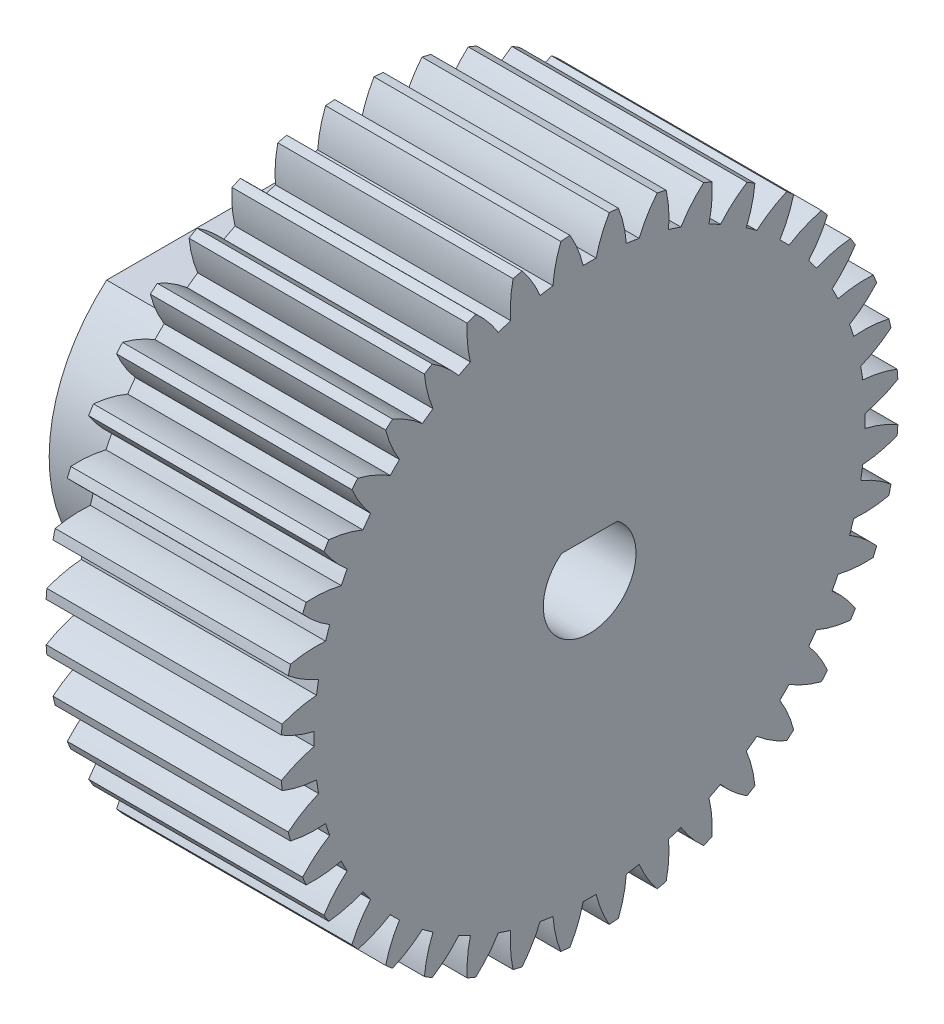
SolidWorks part; units mm, degrees
ref_plane "Plane1" through (0, 0, 0) normal (0, 0, 1) x (1, 0, 0)
ref_plane "Plane2" through (0, 0, 0) normal (0, 1, 0) x (1, 0, 0)
ref_plane "Plane3" through (0, 0, 0) normal (1, 0, 0) x (0, 0, -1)
sketch "HoldingSke" plane through (0, 0, 0) normal (0, 1, 0) x (1, 0, 0)
  line L0 (0, 0) -> (622.6409, -522.4578)
  line L1 (-15, 0) -> (100, 0) construction
  line L2 (0, 0) -> (-2.1039, 2.3779)
  line L3 (0, 0) -> (-11.863, 4.5341)
  line L4 (0, 0) -> (6.6156, 5.5511)
  line L5 (0, 0) -> (-47.5972, -17.7524)
  line L6 (0, 0) -> (-10.5278, -7.1032)
  line L7 (-2.1039, 2.3779) -> (8.8308, 51.9871)
  line L8 (-76.2, 54.61) -> (-71.1708, 54.61)
  line L9 (-71.009, 38.7566) -> (-53.1078, 45.2721)
  line L10 (-76.2, 71.12) -> (104.1128, 71.12)
  line L11 (0, 0) -> (-12.7, 0)
  line L12 (-76.2, 101.6) -> (-76.1716, 101.6)
  line L13 (24.9733, 27.94) -> (52.9518, 28.4284)
  line L14 (24.9733, 27.94) -> (25.0241, 27.9398)
  line L15 (24.9733, 27.94) -> (100.4021, 29.52)
  circle A0 centre (0, 0) radius 2.3812
  circle A1 centre (0, 0) radius 14.8717
  circle A2 centre (0, 0) radius 38.1
  circle A3 centre (0, 0) radius 2.3812
  dimension "MHD" = 29.7434
  dimension "Hub_dia" = 76.2
  dimension "Bore" = 4.7625
  dimension "MBD" = 4.7625
  dimension "Num_teeth" = 40
  dimension "Pitch" = 812.8
  dimension "Overall_len" = 50.8
  dimension "Show_teeth" = 40
  dimension "Thickness" = 12.7
  dimension "OAL" = 50.8001
  dimension "T_dim" = 5.0292
  dimension "Ap" = 20
  dimension "H" = 19.05
  dimension "Pitch_radius" = 180.3128
  dimension "Width" = 12.7
  dimension "Backlash" = 0.0284
  dimension "Addendum_fac" = 1
  dimension "Dedendum_fac" = 1.2
  dimension "Clearance_fac" = 0.2
  dimension "Dedendum_add" = 0.0508
sketch "BasProSke" plane through (0, 0, 0) normal (0, 1, 0) x (1, 0, 0)
  line L0 (-10, 0) -> (60, 0) construction
  line L1 (0, 0) -> (0, 16.6687)
  line L2 (0, 0) -> (12.7, 0)
  line L3 (12.7, 0) -> (12.7, 16.6687)
  line L4 (12.7, 16.6687) -> (0, 16.6687)
  dimension "Thickness" = 12.7
  dimension "Diameter" = 33.3375
revolve "Base-Revolve" add sketch "BasProSke" angle 360 about L0
sketch "TooCutSke" plane through (0, 0, 0) normal (1, 0, 0) x (0, 0, -1)
  line L1 (0, 0) -> (0, 107) construction
  line L2 (0, 0) -> (-0.673, 15.8607) construction
  line L3 (0, 0) -> (-2.4895, 31.6315) construction
  line L4 (-0.673, 15.8607) -> (-1.2447, 15.8157) construction
  arc A0 (0.3509, 14.8676) -> (-0.3509, 14.8676) centre (0, 0) ccw
  arc A1 (1.0752, 16.6595) -> (-1.0752, 16.6595) centre (0, 0) ccw
  circle A2 centre (0, 0) radius 15.875 construction
  circle A3 centre (0, 0) radius 14.9176 construction
  arc A4 (-0.3509, 14.8676) -> (-1.0752, 16.6595) centre (-6.5317, 13.4116) ccw
  arc A5 (1.0752, 16.6595) -> (0.3509, 14.8676) centre (6.5317, 13.4116) ccw
  dimension "Root_dia" = 29.7434
  dimension "Overcut_dia" = 33.3883
  dimension "Pitch_dia" = 31.75
  dimension "Base_dia" = 29.8352
  dimension "Flank_rad" = 6.35
  dimension "Half_ang" = 4.5
  dimension "Half_CT" = 0.5735
extrude "ToothCut" cut sketch "TooCutSke" along normal through all
fillet "Breaks" [suppressed] radius 0.0159
fillet "RootFillets" [suppressed] radius 0.2095
pattern_circular "TeethCuts" count 40 every 9 about axis through (-10, 0, 0) along (1, 0, 0) of "ToothCut", "RootFillets", "Breaks"
sketch "HubNeaOneSke" plane through (0, 0, 0) normal (-1, 0, 0) x (0, 0, 1)
  circle A0 centre (0, 0) radius 14.8717
  dimension "Diameter" = 29.7434
extrude "HubNearOne" [suppressed] add sketch "HubNeaOneSke" along normal blind 38.1001
sketch "HubNeaBotSke" plane through (0, 0, 0) normal (-1, 0, 0) x (0, 0, 1)
  circle A0 centre (0, 0) radius 14.8717
  dimension "Diameter" = 29.7434
extrude "HubNearBoth" [suppressed] add sketch "HubNeaBotSke" along normal blind 19.05
ref_plane "FarPln" through (12.7, 0, 0) normal (1, 0, 0) x (0, 0, -1)
sketch "HubFarSke" plane through (12.7, 0, 0) normal (1, 0, 0) x (0, 0, -1)
  circle A0 centre (0, 0) radius 14.8717
  dimension "Diameter" = 29.7434
extrude "HubFar" [suppressed] add sketch "HubFarSke" along normal blind 19.05
sketch "BorSke" plane through (0, 0, 0) normal (1, 0, 0) x (0, 0, -1)
  circle A0 centre (0, 0) radius 2.3812
  dimension "Diameter" = 4.7625
extrude "Bore" cut sketch "BorSke" along normal mid plane 101.6001
sketch "KeySke" plane through (0, 0, 0) normal (1, 0, 0) x (0, 0, -1)
  line L0 (-0.127, 0) -> (-0.127, 2.6479)
  line L1 (-0.127, 2.6479) -> (0.127, 2.6479)
  line L2 (0.127, 2.6479) -> (0.127, 0)
  line L3 (0, 0) -> (0, 34) construction
  line L4 (-0.127, 0) -> (0.127, 0)
  dimension "Offset" = 2.648
  dimension "Width" = 0.254
extrude "Keyway" [suppressed] cut sketch "KeySke" along normal mid plane 101.6001
pattern_circular "Keyway2" [suppressed] count 2 every 90 about axis through (-10, 0, 0) along (1, 0, 0)
sketch "Sketch1" plane through (12.7, 0, 0) normal (1, 0, 0) x (0, 0, -1)
  line L0 (0, 25.6558) -> (0, -26.1333) construction
  line L1 (-24.8431, 0) -> (25.1424, 0) construction
  line L2 (-20.32, 20.32) -> (-20.32, -20.32) construction
  line L3 (-20.32, -20.32) -> (20.32, -20.32) construction
  line L4 (20.32, -20.32) -> (20.32, 20.32) construction
  line L5 (20.32, 20.32) -> (-20.32, 20.32) construction
  circle A0 centre (-20.32, 20.32) radius 2.413
  circle A1 centre (20.32, 20.32) radius 2.413
  circle A2 centre (20.32, -20.32) radius 2.413
  circle A3 centre (-20.32, -20.32) radius 2.413
  point P7 (0, 20.32)
  point P10 (20.32, 0)
  dimension "D3" = 4.826
  dimension "D1" = 40.64
  dimension "D2" = 40.64
extrude "Cut-Extrude1" cut sketch "Sketch1" against normal up to surface (12.7 mm away)
sketch "Sketch2" plane through (12.7, 0, 0) normal (1, 0, 0) x (0, 0, -1)
  circle A0 centre (0, 0) radius 5.461
  dimension "D1" = 10.922
extrude "Cut-Extrude2" cut sketch "Sketch2" against normal up to surface (12.7 mm away) up to face at (0, 0, -2.3812)
sketch "Sketch3" plane through (12.7, 0, 0) normal (1, 0, 0) x (0, 0, -1)
  line L0 (-20.32, -20.32) -> (20.32, 20.32) construction
  line L1 (-20.32, 20.32) -> (20.32, -20.32) construction
  line L2 (19.794, -28.7742) -> (6.7711, -15.7513)
  line L3 (28.7742, -19.794) -> (15.7513, -6.7711)
  line L4 (-28.7742, -19.794) -> (-15.7513, -6.7711)
  line L5 (-19.794, -28.7742) -> (-6.7711, -15.7513)
  line L6 (-6.7711, 15.7513) -> (-19.794, 28.7742)
  line L7 (6.7711, 15.7513) -> (19.794, 28.7742)
  line L8 (-15.7513, 6.7711) -> (-28.7742, 19.794)
  line L12 (15.7513, 6.7711) -> (28.7742, 19.794)
  arc A0 (-28.7742, 19.794) -> (-28.7742, -19.794) centre (0, 0) ccw
  arc A1 (-15.7513, 6.7711) -> (-15.7513, -6.7711) centre (0, 0) ccw
  arc A2 (-6.7711, -15.7513) -> (6.7711, -15.7513) centre (0, 0) ccw
  arc A3 (15.7513, -6.7711) -> (15.7513, 6.7711) centre (0, 0) ccw
  arc A4 (6.7711, 15.7513) -> (-6.7711, 15.7513) centre (0, 0) ccw
  arc A5 (19.794, 28.7742) -> (-19.794, 28.7742) centre (0, 0) ccw
  arc A6 (28.7742, -19.794) -> (28.7742, 19.794) centre (0, 0) ccw
  arc A7 (-19.794, -28.7742) -> (19.794, -28.7742) centre (0, 0) ccw
  dimension "D1" = 69.85
  dimension "D2" = 17.78
  dimension "D3" = 12.7
  dimension "D4" = 12.7
extrude "Cut-Extrude3" cut sketch "Sketch3" against normal up to surface (12.7 mm away)
sketch "Sketch4" plane through (12.7, 0, 0) normal (1, 0, 0) x (0, 0, -1)
  circle A0 centre (0, 0) radius 2.5019
  circle A1 centre (0, 0) radius 5.461
  circle A2 centre (0, 0) radius 5.461 construction
  dimension "D1" = 5.0038
extrude "Boss-Extrude1" add sketch "Sketch4" against normal up to surface (12.7 mm away) up to face at (0, 0, -5.461)
sketch "Sketch5" plane through (12.7, 0, 0) normal (1, 0, 0) x (0, 0, -1)
  line L0 (-1.5112, 1.9939) -> (1.5112, 1.9939)
  line L1 (-1.6042, -2.5019) -> (1.6042, -2.5019) construction
  circle A0 centre (0, 0) radius 2.5019 construction
  arc A1 (-1.5112, 1.9939) -> (1.5112, 1.9939) centre (0, 0) cw
  point P6 (0, -2.5019)
  point P7 (0, 1.9939)
  dimension "D1" = 4.4958
extrude "Boss-Extrude2" add sketch "Sketch5" against normal up to surface (12.7 mm away) up to face at (0, 0, 0)
sketch "Sketch6" plane through (0, 0, 0) normal (-1, 0, 0) x (0, 0, 1)
  line L0 (-5.7489, 6.731) -> (5.7489, 6.731)
  line L1 (-1.5112, 1.9939) -> (1.5112, 1.9939) construction
  circle A0 centre (0, 0) radius 2.5019
  arc A1 (-1.5112, 1.9939) -> (1.5112, 1.9939) centre (0, 0) ccw construction
  arc A2 (-5.7489, 6.731) -> (5.7489, 6.731) centre (0, 0) ccw
  point P11 (0, 1.9939)
  point P12 (0, 6.731)
  dimension "D1" = 6.35
  dimension "D2" = 6.731
extrude "Boss-Extrude3" add sketch "Sketch6" along normal blind 7.62
sketch "Sketch8" plane through (0, 6.731, 0) normal (0, 1, 0) x (1, 0, 0)
  line L0 (0, -5.7489) -> (0, 5.7489) construction
  circle A0 centre (-3.81, 0) radius 1.7526
  point P4 (0, 0)
  point P5 (0, 0)
  dimension "D1" = 3.5052
  dimension "D2" = 3.81
extrude "Cut-Extrude4" cut sketch "Sketch8" against normal up to surface (4.9455 mm away)
equation "' \"Pitch@HoldingSke\" = 4"
equation "' \"Num_teeth@HoldingSke\" = 12"
equation "' \"Ap@HoldingSke\" =  20"
equation "' \"Ap@HoldingSke\" = 20"
equation "' \"Width@HoldingSke\" = 0.5"
equation "' \"Hub_dia@HoldingSke\"= 1"
equation "' \"Hub_dia@HoldingSke\" = 1"
equation "' \"Overall_len@HoldingSke\" = 1.0"
equation "' \"Bore@HoldingSke\" = 0.75"
equation "' \"T_dim@HoldingSke\" = 0.85"
equation "' \"Width@KeySke\" = 0.25"
equation "' \"Show_teeth@HoldingSke\" = 13"
equation "' \"Backlash@HoldingSke\" = 0.009"
equation "' \"Addendum_fac@HoldingSke\" = 1.0"
equation "' \"Dedendum_fac@HoldingSke\" = 1.25"
equation "' \"Dedendum_add@HoldingSke\" = 0.00005"
equation "' \"Clearance_fac@HoldingSke\" = 0.25"
equation "' \"Pitch@HoldingSke\" = 0.5"
equation "' \"Num_teeth@HoldingSke\" = 23"
equation "' \"Show_teeth@HoldingSke\" = 23"
equation "' \"Backlash@HoldingSke\" = 0.0375"
equation "\"Overcut_dia@TooCutSke\" = (\"Num_teeth@HoldingSke\" + 2 * \"Addendum_fac@HoldingSke\") / \"Pitch@HoldingSke\" + 0.002"
equation "\"Pitch_dia@TooCutSke\" = \"Num_teeth@HoldingSke\" / \"Pitch@HoldingSke\""
equation "\"Base_dia@TooCutSke\" = \"Num_teeth@HoldingSke\" / \"Pitch@HoldingSke\" * cos((\"Ap@HoldingSke\"  * 3.14159265 / 180))"
equation "\"Root_dia@TooCutSke\" = (\"Num_teeth@HoldingSke\" + 2) / \"Pitch@HoldingSke\" - 2 * (\"Addendum_fac@HoldingSke\" + \"Dedendum_fac@HoldingSke\") / \"Pitch@HoldingSke\" - \"Dedendum_add@HoldingSke\" * 2"
equation "\"Half_ang@TooCutSke\" = 180 / \"Num_teeth@HoldingSke\""
equation "\"Half_CT@TooCutSke\" = \"Num_teeth@HoldingSke\" / \"Pitch@HoldingSke\" * sin((3.14159265 / 2 / \"Num_teeth@HoldingSke\")) / 2 - 7 * \"Backlash@HoldingSke\" / 4"
equation "\"Flank_rad@TooCutSke\" = \"Num_teeth@HoldingSke\" / \"Pitch@HoldingSke\" / 5"
equation "\"Radius@RootFillets\" = \"Clearance_fac@HoldingSke\" / \"Pitch@HoldingSke\" + \"Dedendum_add@HoldingSke\""
equation "\"Break_rad@Breaks\" = 0.02 / \"Pitch@HoldingSke\""
equation "\"Thickness@HoldingSke\" = \"Width@HoldingSke\""
equation "\"OAL@HoldingSke\" = \"Thickness@HoldingSke\""
equation "\"MHD@HoldingSke\" = (\"Num_teeth@HoldingSke\" + 2) / \"Pitch@HoldingSke\" - 2 * (\"Addendum_fac@HoldingSke\" + \"Dedendum_fac@HoldingSke\")  / \"Pitch@HoldingSke\" - \"Dedendum_add@HoldingSke\" * 2"
equation "\"MBD@HoldingSke\" = (\"Num_teeth@HoldingSke\" + 2) / \"Pitch@HoldingSke\" - 2 * (\"Addendum_fac@HoldingSke\" + \"Dedendum_fac@HoldingSke\")  / \"Pitch@HoldingSke\" - \"Dedendum_add@HoldingSke\" * 2 - 0.002"
equation "\"MHD@HoldingSke\" = ((sgn( \"MHD@HoldingSke\" - \"Hub_dia@HoldingSke\" )-1)*( \"MHD@HoldingSke\" - \"Hub_dia@HoldingSke\" ))/-2+ \"Hub_dia@HoldingSke\""
equation "\"MBD@HoldingSke\" = ((sgn( \"MBD@HoldingSke\" - \"Bore@HoldingSke\" )-1)*( \"MBD@HoldingSke\" - \"Bore@HoldingSke\" ))/-2+ \"Bore@HoldingSke\""
equation "\"OAL@HoldingSke\" = ((sgn( \"OAL@HoldingSke\" - \"Overall_len@HoldingSke\" )+1)*( \"OAL@HoldingSke\" - \"Overall_len@HoldingSke\" ))/2 + \"Overall_len@HoldingSke\" + 0.000002"
equation "\"Num_teeth@TeethCuts\" = int( \"Show_teeth@HoldingSke\" ) + 1"
equation "\"Num_teeth@TeethCuts\" = ((sgn( \"Num_teeth@TeethCuts\" - \"Num_teeth@HoldingSke\" )-1)*( \"Num_teeth@TeethCuts\" - \"Num_teeth@HoldingSke\" ))/-2+ \"Num_teeth@HoldingSke\""
equation "\"Num_teeth@TeethCuts\" = ((sgn( \"Num_teeth@TeethCuts\" - 2.0)+1)*( \"Num_teeth@TeethCuts\" - 2.0))/2 +2.0"
equation "\"Angle@TeethCuts\" = 360.0 / \"Num_teeth@HoldingSke\""
equation "\"Diameter@BasProSke\" = (\"Num_teeth@HoldingSke\" + 2 * \"Addendum_fac@HoldingSke\") / \"Pitch@HoldingSke\""
equation "\"Thickness@BasProSke\"  = \"Thickness@HoldingSke\""
equation "' \"Fillet_rad@BasProSke\" =  \"Thickness@HoldingSke\" * 0.05"
equation "' \"Fillet_rad@BasProSke\" = \"Thickness@HoldingSke\" * 0.05"
equation "\"MHD@HoldingSke\" = ((sgn( \"MHD@HoldingSke\" - \"Root_dia@TooCutSke\" )-1)*( \"MHD@HoldingSke\" - \"Root_dia@TooCutSke\" ))/-2+ \"Root_dia@TooCutSke\""
equation "\"Diameter@HubNeaOneSke\" = \"MHD@HoldingSke\""
equation "\"Length@HubNearOne\" = \"OAL@HoldingSke\" - \"Thickness@BasProSke\""
equation "\"Diameter@HubNeaBotSke\" = \"MHD@HoldingSke\""
equation "\"Length@HubNearBoth\" = ( \"OAL@HoldingSke\" - \"Thickness@BasProSke\" ) / 2.0"
equation "\"Thickness@FarPln\" = \"Thickness@BasProSke\""
equation "\"Diameter@HubFarSke\" = \"MHD@HoldingSke\""
equation "\"Length@HubFar\" = ( \"OAL@HoldingSke\" - \"Thickness@BasProSke\" ) / 2.0"
equation "\"Diameter@BorSke\" = \"MBD@HoldingSke\""
equation "\"D1@Bore\" = \"OAL@HoldingSke\" * 2.0"
equation "\"D1@Keyway\" = \"OAL@HoldingSke\" * 2.0"
equation "\"Offset@KeySke\" = \"T_dim@HoldingSke\" - \"MBD@HoldingSke\" / 2.0"
equation "\"o.5\"=0.672596"
